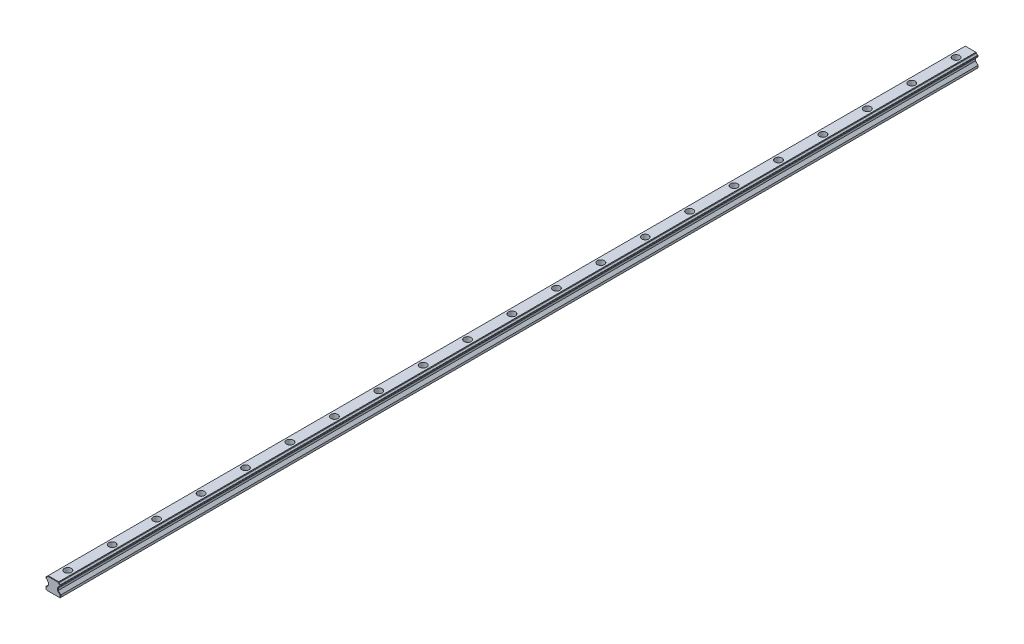
SolidWorks part; units mm, degrees
ref_plane "Front Plane" through (0, 0, 0) normal (0, 0, 1) x (1, 0, 0)
ref_plane "Top Plane" through (0, 0, 0) normal (0, 1, 0) x (1, 0, 0)
ref_plane "Right Plane" through (0, 0, 0) normal (1, 0, 0) x (0, 0, -1)
sketch "Sketch1" plane through (-20, 0, 0) normal (0, 0, 1) x (1, 0, 0)
  line L0 (10, -4.9999) -> (10, -8)
  line L1 (10, -8) -> (11, -9)
  line L2 (11, -9) -> (20, -9)
  line L3 (17, 9) -> (23, 9)
  line L5 (26.55, -1.55) -> (30, -4.9999)
  line L6 (26.55, 1.3792) -> (26.55, -1.55)
  line L7 (27.7679, 2.5951) -> (26.55, 1.3792)
  line L8 (30, 4.8292) -> (29.4727, 4.3144)
  line L9 (30, 6.16) -> (30, 4.8292)
  line L10 (29.4727, 6.6874) -> (30, 6.16)
  line L11 (27.16, 9) -> (27.7679, 8.3921)
  line L13 (29, -9) -> (20, -9)
  line L14 (30, -8) -> (29, -9)
  line L15 (30, -4.9999) -> (30, -8)
  line L16 (27.16, 9) -> (12.84, 9)
  line L17 (12.84, 9) -> (12.2321, 8.3921)
  line L18 (10.5273, 6.6874) -> (10, 6.16)
  line L19 (10, 6.16) -> (10, 4.8292)
  line L20 (10, 4.8292) -> (10.5273, 4.3144)
  line L21 (12.2321, 2.5951) -> (13.45, 1.3792)
  line L22 (13.45, 1.3792) -> (13.45, -1.55)
  line L23 (13.45, -1.55) -> (10, -4.9999)
  line L25 (20, -9) -> (20, 9) construction
  arc A0 (29.4727, 4.3144) -> (27.7679, 2.5951) centre (29.8039, 2.2812) ccw
  arc A1 (27.7679, 8.3921) -> (29.4727, 6.6874) centre (29.8015, 8.7209) ccw
  arc A2 (12.2321, 8.3921) -> (10.5273, 6.6874) centre (10.1985, 8.7209) cw
  arc A3 (10.5273, 4.3144) -> (12.2321, 2.5951) centre (10.1961, 2.2812) cw
  point P3 (20, 0.5)
  point P37 (20, 0)
  point P42 (20, 9)
  dimension "D17" = 2.06
  dimension "Rail Width" = 20
  dimension "D2" = 1
  dimension "D3" = 1
  dimension "D4" = 6
  dimension "D7" = 18
  dimension "D8" = 4.0001
  dimension "D9" = 10.55
  dimension "D10" = 13.1001
  dimension "D11" = 15.5359
  dimension "D12" = 0.6079
  dimension "D13" = 0.6079
  dimension "D15" = 0.5273
  dimension "D16" = 0.5273
  dimension "D18" = 1.2159
  dimension "D19" = 0.5148
  dimension "D20" = 6.4049
  dimension "D21" = 2.84
  dimension "D22" = 4.1708
  dimension "Rail Height" = 18
  dimension "Mounting Hole Dpeth" = 8.5
sketch "Sketch2" plane through (0, 0, 0) normal (1, 0, 0) x (0, 0, -1)
  line L0 (-600, 9) -> (-595.25, 9)
  line L1 (-595.25, 9) -> (-595.25, 0.5)
  line L2 (-595.25, 0.5) -> (-597, 0.5)
  line L3 (-597, 0.5) -> (-597, -9)
  line L4 (-597, -9) -> (-600, -9)
  line L5 (-600, -9) -> (-600, 9) construction
  line L6 (-600, -9) -> (-600, 9) construction
  line L7 (530, 0) -> (-530, 0)
  line L9 (-600, 9) -> (-600, -9)
  line L10 (620, 0) -> (-620, 0) construction
  point P6 (-480, 0)
  point P7 (-600, 0)
  point P8 (-420, 0)
  point P11 (0, 0)
  point P12 (-540, 0)
  point P13 (-300, 0)
  point P14 (-530, 0)
  point P18 (-240, 0)
  point P21 (0, 0)
  point P22 (530, 0)
  point P24 (-360, 0)
  point P25 (-180, 0)
  point P26 (-120, 0)
  point P27 (-60, 0)
  point P28 (0, 0)
  point P29 (60, 0)
  point P30 (120, 0)
  point P31 (180, 0)
  point P32 (240, 0)
  point P33 (300, 0)
  point P34 (360, 0)
  point P35 (530, -1)
  point P36 (420, 0)
  point P37 (480, 0)
  point P38 (540, 0)
  point P39 (600, 0)
  dimension "D1" = 9.5
  dimension "D3" = 6
  dimension "Rail Length" = 1240
  dimension "Mounting Hole Center-to-End" = 20
  dimension "Mounting Hole Center-to-Center" = 60
  dimension "D2" = 90
  dimension "D4" = 1
  dimension "Number of Mounting Holes" = 21
sketch "Sketch3" plane through (0, 0, 0) normal (0, 0, 1) x (1, 0, 0)
  line L0 (-3, 9) -> (3, 9) construction
  line L3 (-3, 9) -> (3, 9)
  line L21 (0, -9) -> (9, -9)
  line L22 (9, -9) -> (10, -8)
  line L23 (10, -8) -> (10, -4.9999)
  line L24 (10, -4.9999) -> (6.55, -1.55)
  line L25 (6.55, -1.55) -> (6.55, 1.3792)
  line L26 (6.55, 1.3792) -> (7.7679, 2.5951)
  line L27 (9.4727, 4.3144) -> (10, 4.8292)
  line L28 (10, 4.8292) -> (10, 6.16)
  line L29 (10, 6.16) -> (9.4727, 6.6874)
  line L30 (7.7679, 8.3921) -> (7.16, 9)
  line L31 (7.16, 9) -> (-7.16, 9)
  line L32 (-7.16, 9) -> (-7.7679, 8.3921)
  line L33 (-9.4727, 6.6874) -> (-10, 6.16)
  line L34 (-10, 6.16) -> (-10, 4.8292)
  line L35 (-10, 4.8292) -> (-9.4727, 4.3144)
  line L36 (-7.7679, 2.5951) -> (-6.55, 1.3792)
  line L37 (-6.55, 1.3792) -> (-6.55, -1.55)
  line L38 (-6.55, -1.55) -> (-10, -4.9999)
  line L39 (-10, -4.9999) -> (-10, -8)
  line L40 (-10, -8) -> (-9, -9)
  line L41 (-9, -9) -> (0, -9)
  line L42 (0, -9) -> (9, -9)
  line L43 (9, -9) -> (10, -8)
  line L44 (10, -8) -> (10, -4.9999)
  line L45 (10, -4.9999) -> (6.55, -1.55)
  line L46 (6.55, -1.55) -> (6.55, 1.3792)
  line L47 (6.55, 1.3792) -> (7.7679, 2.5951)
  line L48 (9.4727, 4.3144) -> (10, 4.8292)
  line L49 (10, 4.8292) -> (10, 6.16)
  line L50 (10, 6.16) -> (9.4727, 6.6874)
  line L51 (7.7679, 8.3921) -> (7.16, 9)
  line L52 (7.16, 9) -> (-7.16, 9)
  line L53 (-7.16, 9) -> (-7.7679, 8.3921)
  line L54 (-9.4727, 6.6874) -> (-10, 6.16)
  line L55 (-10, 6.16) -> (-10, 4.8292)
  line L56 (-10, 4.8292) -> (-9.4727, 4.3144)
  line L57 (-7.7679, 2.5951) -> (-6.55, 1.3792)
  line L58 (-6.55, 1.3792) -> (-6.55, -1.55)
  line L59 (-6.55, -1.55) -> (-10, -4.9999)
  line L60 (-10, -4.9999) -> (-10, -8)
  line L61 (-10, -8) -> (-9, -9)
  line L62 (-9, -9) -> (0, -9)
  arc A4 (9.4727, 4.3144) -> (7.7679, 2.5951) centre (9.8039, 2.2812) ccw
  arc A5 (7.7679, 8.3921) -> (9.4727, 6.6874) centre (9.8015, 8.7209) ccw
  arc A6 (-9.4727, 6.6874) -> (-7.7679, 8.3921) centre (-9.8015, 8.7209) ccw
  arc A7 (-7.7679, 2.5951) -> (-9.4727, 4.3144) centre (-9.8039, 2.2812) ccw
  arc A8 (9.4727, 4.3144) -> (7.7679, 2.5951) centre (9.8039, 2.2812) ccw
  arc A9 (7.7679, 8.3921) -> (9.4727, 6.6874) centre (9.8015, 8.7209) ccw
  arc A10 (-9.4727, 6.6874) -> (-7.7679, 8.3921) centre (-9.8015, 8.7209) ccw
  arc A11 (-7.7679, 2.5951) -> (-9.4727, 4.3144) centre (-9.8039, 2.2812) ccw
  dimension "D1" = 0
extrude "Boss-Extrude1" add sketch "Sketch3" along normal up to vertex (620 mm away) and the other way up to vertex (620 mm away) contours A11 L57 L58 L59 L60 L61 L62 L42 L43 L44 L45 L46 L47 A8 L48 L49 L50 A9 L51 L52 L3 L53 A10 L54 L55 L56 up to point (0, 0, 620) other way up to point (0, 0, -620)
sketch "Sketch4" plane through (0, 0, 0) normal (1, 0, 0) x (0, 0, -1)
  line L6 (-595.25, 9) -> (-600, 9)
  line L7 (-595.25, 0.5) -> (-595.25, 9)
  line L8 (-597, 0.5) -> (-595.25, 0.5)
  line L9 (-597, -9) -> (-597, 0.5)
  line L10 (-600, -9) -> (-597, -9)
  line L11 (-600, 9) -> (-600, -9)
  line L12 (-595.25, 9) -> (-600, 9)
  line L13 (-595.25, 0.5) -> (-595.25, 9)
  line L14 (-597, 0.5) -> (-595.25, 0.5)
  line L15 (-597, -9) -> (-597, 0.5)
  line L16 (-600, -9) -> (-597, -9)
  line L17 (-600, 9) -> (-600, -9)
  dimension "D1" = 0
revolve "Cut-Revolve1" cut sketch "Sketch4" angle 360 about L17
pattern_linear "LPattern2" count 21 spacing 60 along (0, 0, -1) of "Cut-Revolve1"
sketch "Sketch5" plane through (0, 0, 0) normal (0, 1, 0) x (1, 0, 0)
  line L0 (3, -600) -> (0, -600) construction
  line L1 (0, -600) -> (2.1213, -597.8787) construction
  circle A1 centre (0, -600) radius 3 construction
  circle A2 centre (0, -600) radius 3 construction
  point P3 (0, -603)
  point P4 (-3, -600)
  point P6 (3, -600)
  point P7 (2.1213, -597.8787)
  dimension "D1" = 45
sketch "Sketch6" plane through (0, 0, 0) normal (0, 0, 1) x (1, 0, 0)
  line L0 (4.75, 9) -> (-4.75, 9) construction
  line L1 (3, 0.5) -> (-3, 0.5) construction
  line L2 (4.75, 9) -> (-4.75, 9) construction
  line L3 (3, 0.5) -> (-3, 0.5) construction
  line L4 (-4.75, 9) -> (-4.75, 0.5)
  line L5 (-4.75, 0.5) -> (-3, 0.5)
  line L6 (4.75, 9) -> (4.75, 0.5)
  line L7 (4.75, 0.5) -> (3, 0.5)
  line L8 (3, 0.5) -> (3, -9)
  line L9 (-9, -9) -> (9, -9) construction
  line L10 (-3, 0.5) -> (-3, -9)
chamfer "Chamfer1" distance 0.5 angle 45 48 edges at (-7.159, 1.9872, -620) (-6.55, -0.0854, -620) (-8.275, -3.275, -620) (-10, -6.5, -620) (-9.5, -8.5, -620) (0, -9, -620) (9.5, -8.5, -620) (10, -6.5, -620) (8.275, -3.275, -620) (6.55, -0.0854, -620) (7.159, 1.9872, -620) (8.3411, 3.7316, -620) (9.7363, 4.5718, -620) (10, 5.4946, -620) (9.7363, 6.4237, -620) (8.3449, 7.2643, -620) (7.464, 8.6961, -620) (0, 9, -620) (-7.464, 8.6961, -620) (-8.3449, 7.2643, -620) (-9.7363, 6.4237, -620) (-10, 5.4946, -620) (-9.7363, 4.5718, -620) (-8.3411, 3.7316, -620) (-9.7363, 4.5718, 620) (-10, 5.4946, 620) (-9.7363, 6.4237, 620) (-8.3449, 7.2643, 620) (-7.464, 8.6961, 620) (0, 9, 620) (7.464, 8.6961, 620) (8.3449, 7.2643, 620) (9.7363, 6.4237, 620) (10, 5.4946, 620) (9.7363, 4.5718, 620) (8.3411, 3.7316, 620) (7.159, 1.9872, 620) (6.55, -0.0854, 620) (8.275, -3.275, 620) (10, -6.5, 620) (9.5, -8.5, 620) (0, -9, 620) (-9.5, -8.5, 620) (-10, -6.5, 620) (-8.275, -3.275, 620) (-6.55, -0.0854, 620) (-7.159, 1.9872, 620) (-8.3411, 3.7316, 620)
equation "\"D3@LPattern2\"=\"Mounting Hole Center-to-Center@Sketch2\""
equation "\"D1@LPattern2\"=\"Number of Mounting Holes@Sketch2\""
